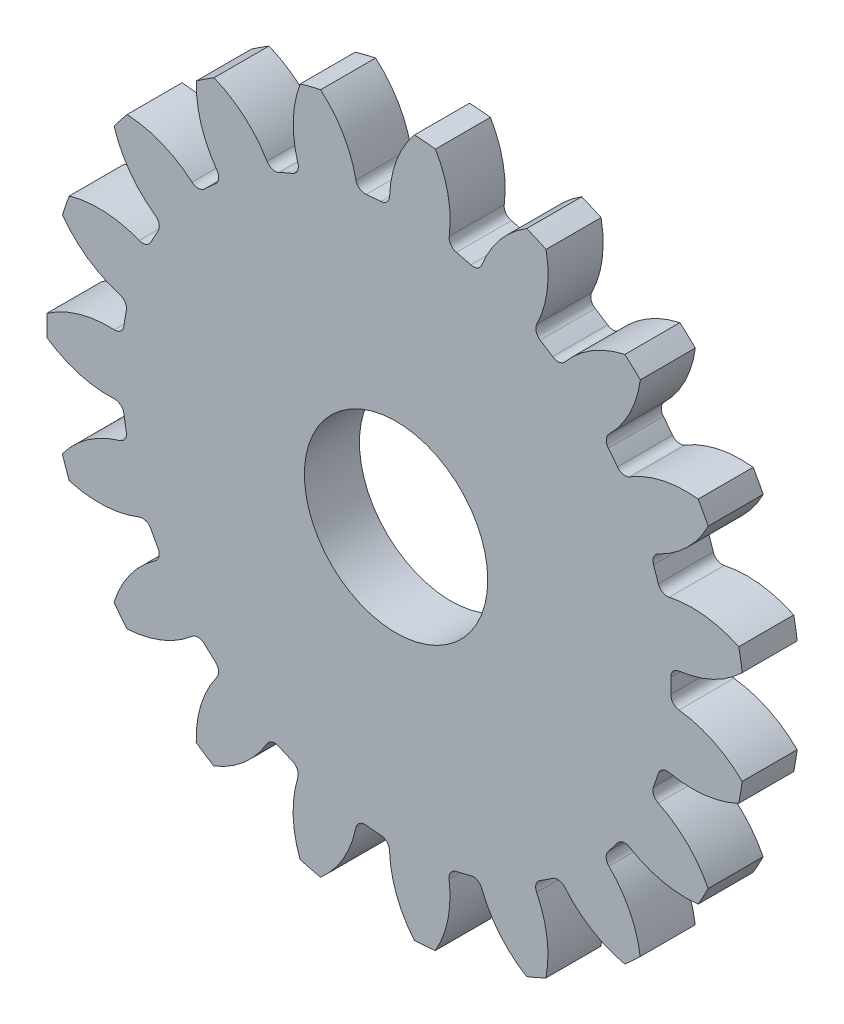
SolidWorks part; units mm, degrees
ref_plane "Alzado" through (0, 0, 0) normal (0, 0, 1) x (1, 0, 0)
ref_plane "Planta" through (0, 0, 0) normal (0, 1, 0) x (1, 0, 0)
ref_plane "Vista lateral" through (0, 0, 0) normal (1, 0, 0) x (0, 0, -1)
sketch "Croquis1" plane through (0, 0, 0) normal (0, 0, 1) x (1, 0, 0)
  circle A0 centre (0, 0) radius 19.05
  dimension "D1" = 38.1
extrude "Saliente-Extruir1" add sketch "Croquis1" along normal blind 3
sketch "Croquis2" plane through (0, 0, 3) normal (0, 0, 1) x (1, 0, 0)
  line L0 (0, 0) -> (0, 17.272) construction
  line L1 (0, 0) -> (6.8197, 18.737) construction
  line L2 (0, 0) -> (-1.4224, 17.2133) construction
  line L3 (0, 17.272) -> (5.5511, 15.2516) construction
  arc A0 (1.0047, 19.0235) -> (-4.1137, 18.6005) centre (0, 0) ccw
  arc A2 (-0.3501, 14.9819) -> (-2.1139, 14.8362) centre (0, 0) ccw
  arc A3 (1.0047, 19.0235) -> (-0.3501, 14.9819) centre (5.5511, 15.2516) ccw
  arc A4 (-4.1137, 18.6005) -> (-2.1139, 14.8362) centre (-7.9793, 14.1335) cw
  dimension "D2" = 29.972
  dimension "D3" = 20
  dimension "D4" = 1.4224
extrude "Cortar-Extruir1" cut sketch "Croquis2" against normal through all
fillet "Redondeo1" radius 0.508 2 edges at (-0.3501, 14.9819, 1.5) (-2.1139, 14.8362, 1.5)
pattern_circular "MatrizC1" count 19 over 360 about axis through (0, 0, 0) along (0, 0, 1) of "Redondeo1", "Cortar-Extruir1"
sketch "Croquis3" plane through (0, 0, 3) normal (0, 0, 1) x (1, 0, 0)
  circle A0 centre (0, 0) radius 5
  dimension "D1" = 10
extrude "Cortar-Extruir2" cut sketch "Croquis3" against normal through all
